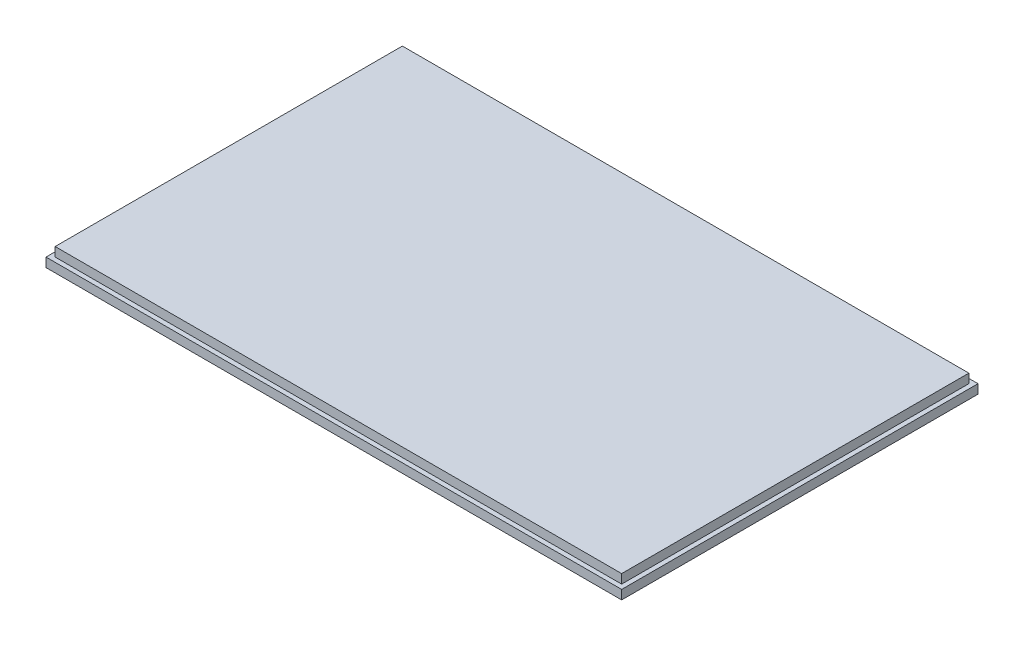
SolidWorks part; units mm, degrees
material "6061-T6 (SS)"
ref_plane "Front Plane" through (0, 0, 0) normal (0, 0, 1) x (1, 0, 0)
ref_plane "Top Plane" through (0, 0, 0) normal (0, 1, 0) x (1, 0, 0)
ref_plane "Right Plane" through (0, 0, 0) normal (1, 0, 0) x (0, 0, -1)
sketch "Sketch1" plane through (0, 0, 0) normal (0, 1, 0) x (1, 0, 0)
  line L1 (-100.0125, -61.9125) -> (100.0125, -61.9125)
  line L2 (-100.0125, -61.9125) -> (-100.0125, 61.9125)
  line L3 (-100.0125, 61.9125) -> (100.0125, 61.9125)
  line L4 (100.0125, -61.9125) -> (100.0125, 61.9125)
  line L5 (-100.0125, -61.9125) -> (100.0125, 61.9125) construction
  line L6 (-100.0125, 61.9125) -> (100.0125, -61.9125) construction
  point P0 (0, 0)
  dimension "D1" = 200.025
  dimension "D2" = 123.825
extrude "Boss-Extrude1" add sketch "Sketch1" along normal blind 3.175
sketch "Sketch2" plane through (0, 3.175, 0) normal (0, 1, 0) x (1, 0, 0)
  line L14 (98.425, -60.325) -> (98.425, 60.325)
  line L15 (-98.425, -60.325) -> (98.425, -60.325)
  line L16 (-98.425, 60.325) -> (-98.425, -60.325)
  line L17 (98.425, 60.325) -> (-98.425, 60.325)
  line L18 (98.425, -60.325) -> (98.425, 60.325)
  line L19 (-98.425, -60.325) -> (98.425, -60.325)
  line L20 (-98.425, 60.325) -> (-98.425, -60.325)
  line L21 (98.425, 60.325) -> (-98.425, 60.325)
  dimension "D1" = 1.5875
extrude "Boss-Extrude2" add sketch "Sketch2" along normal blind 3.175
